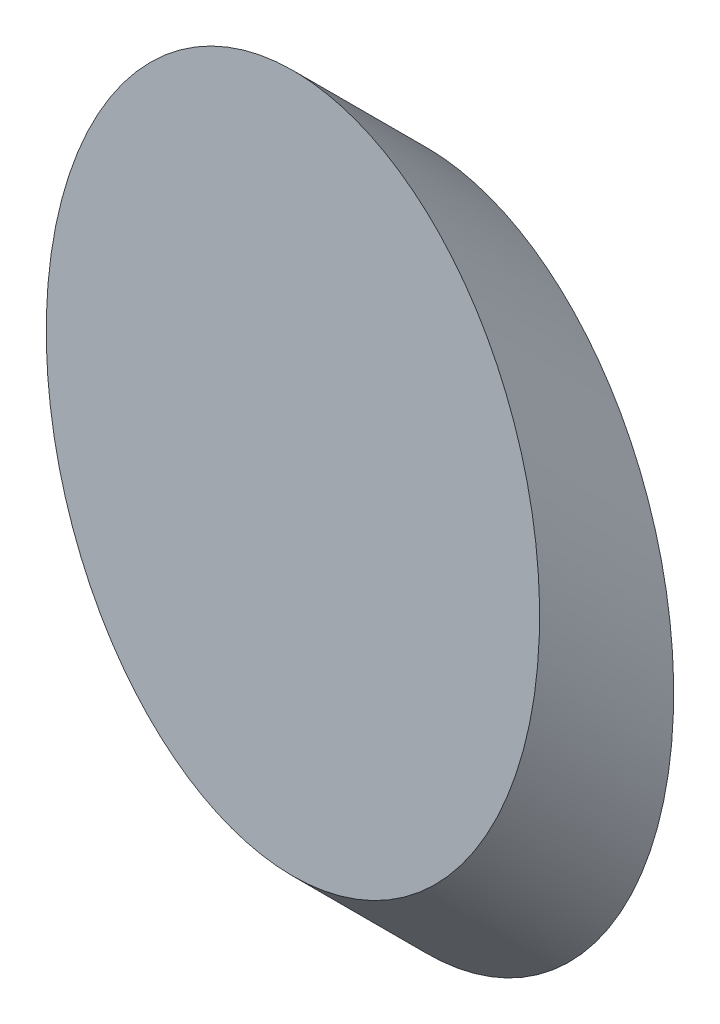
SolidWorks part; units mm, degrees
ref_plane "前视基准面" through (0, 0, 0) normal (0, 0, 1) x (1, 0, 0)
ref_plane "上视基准面" through (0, 0, 0) normal (0, 1, 0) x (1, 0, 0)
ref_plane "右视基准面" through (0, 0, 0) normal (1, 0, 0) x (0, 0, -1)
sketch "草图1" plane through (0, 0, 0) normal (0, 0, 1) x (1, 0, 0)
  ellipse E0 centre (54.3924, 35.7889) end of major axis (54.3924, 68.3189) minor radius 23
  dimension "D1" = 46
  dimension "D2" = 65.06
sketch3d "3D草图2"
  line L0 (55.1123, 68.3029, 0) -> (55.1123, 68.3029, -2.7888)
  line L3 (55.1123, 68.3029, 0) -> (55.1123, 64.7657, -3.5372)
  line L4 (55.1123, 68.3029, 0) -> (55.1123, 28.9476, 0)
  spline S2 degree 3 poles (54.3924, 68.3189, 0) (8.3924, 68.3189, 0) (8.3924, 3.2589, 0) (54.3924, 3.2589, 0) (100.3924, 3.2589, 0) (100.3924, 68.3189, 0) (54.3924, 68.3189, 0) (8.3924, 68.3189, 0) (8.3924, 3.2589, 0) knots -0.5 0 0 0 0.5 0.5 0.5 1 1 1 1.5 1.5 1.5 weights 1 0.333333 0.333333 1 0.333333 0.333333 1 0.333333 0.333333 only from (54.3924, 68.3189, 0) to (54.3924, 68.3189, 0) construction
  dimension "D1" = 45
extrude "凸台-拉伸2" add sketch "草图1" along direction (0, -0.7071, -0.7071) on the side of the normal blind 17.68
